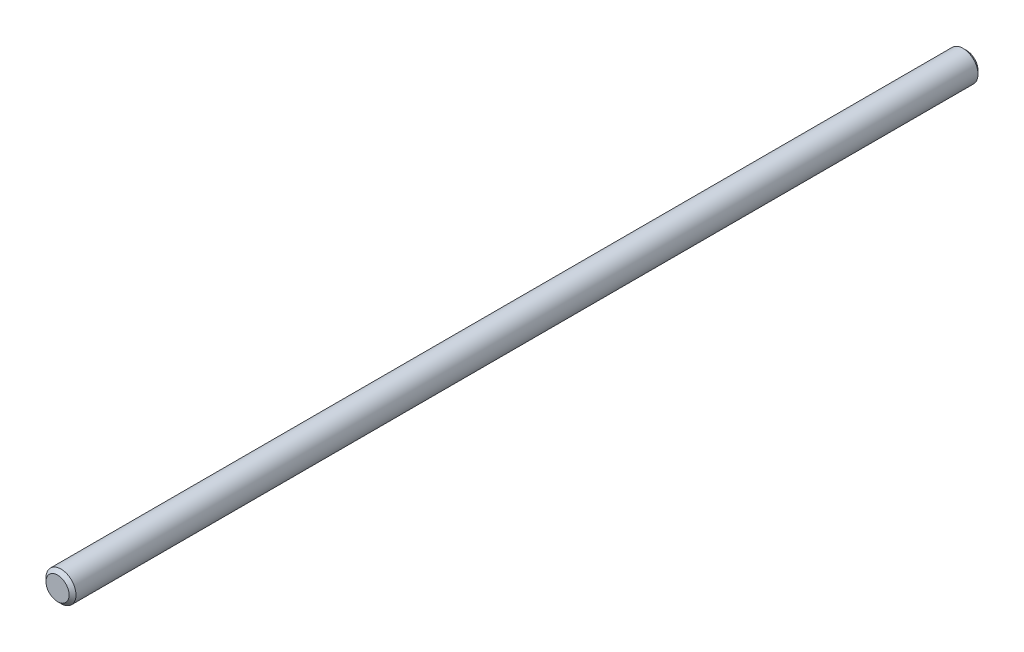
SolidWorks part; units mm, degrees
ref_plane "Front Plane" through (0, 0, 0) normal (0, 0, 1) x (1, 0, 0)
ref_plane "Top Plane" through (0, 0, 0) normal (0, 1, 0) x (1, 0, 0)
ref_plane "Right Plane" through (0, 0, 0) normal (1, 0, 0) x (0, 0, -1)
sketch "Sketch1" plane through (0, 0, 0) normal (0, 0, 1) x (1, 0, 0)
  circle A0 centre (0, 0) radius 13
extrude "Boss-Extrude1" add sketch "Sketch1" along normal blind 787.5
chamfer "Chamfer1" distance 3 angle 45 2 edges at (13, 0, 0) (13, 0, 787.5)
